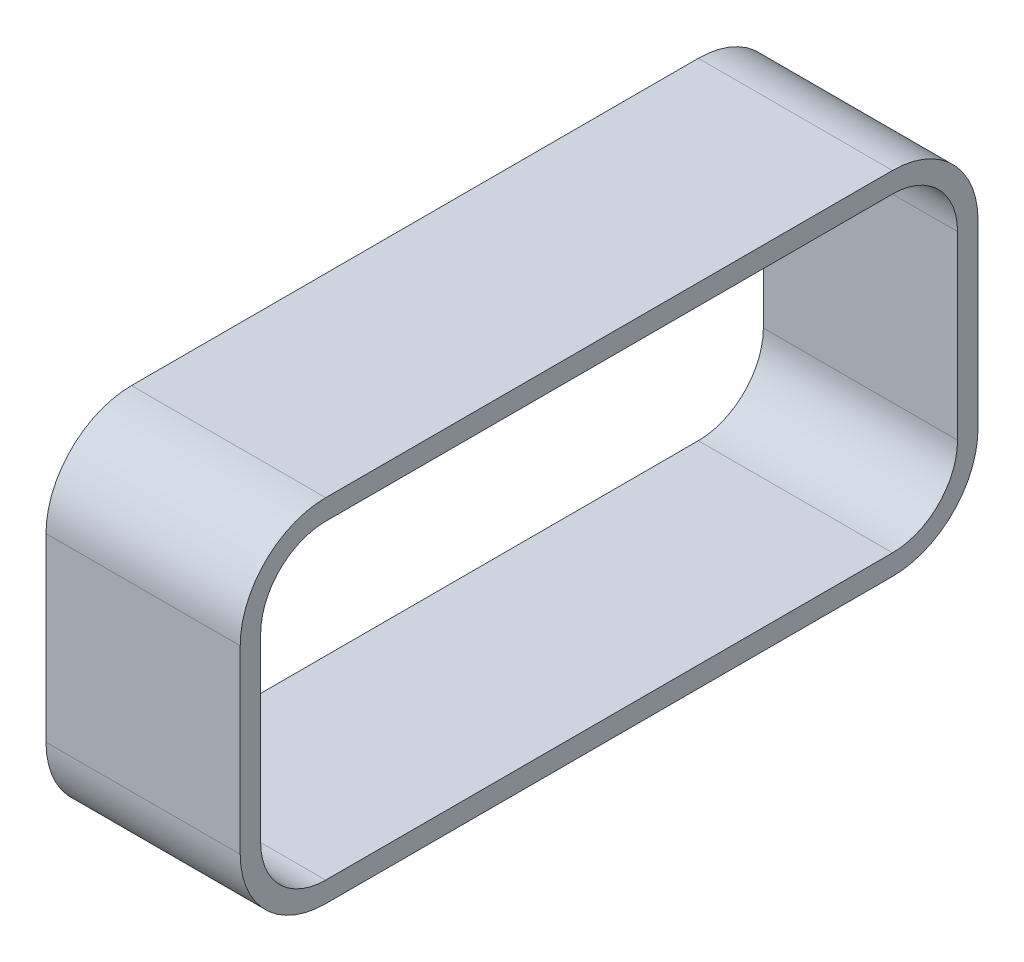
SolidWorks part; units mm, degrees
ref_plane "Front Plane" through (0, 0, 0) normal (0, 0, 1) x (1, 0, 0)
ref_plane "Top Plane" through (0, 0, 0) normal (0, 1, 0) x (1, 0, 0)
ref_plane "Right Plane" through (0, 0, 0) normal (1, 0, 0) x (0, 0, -1)
sketch "Sketch1" plane through (0, 0, 0) normal (1, 0, 0) x (0, 0, -1)
  line L0 (0, 0) -> (3050, 0)
  line L1 (-460, 1322) -> (-460, 350)
  line L2 (3050, 1672) -> (0, 1672)
  line L3 (3400, 1322) -> (3400, 350)
  line L4 (0, 1782) -> (3050, 1782)
  line L5 (3510, 1322) -> (3510, 350)
  line L6 (3050, -110) -> (0, -110)
  line L7 (-350, 350) -> (-350, 1322)
  arc A0 (3050, 0) -> (3400, 350) centre (3050, 350) ccw
  arc A1 (3050, 1672) -> (3400, 1322) centre (3050, 1322) cw
  arc A2 (3050, 1782) -> (3510, 1322) centre (3050, 1322) cw
  arc A3 (3510, 350) -> (3050, -110) centre (3050, 350) cw
  arc A4 (0, 0) -> (-350, 350) centre (0, 350) cw
  arc A5 (-350, 1322) -> (0, 1672) centre (0, 1322) cw
  arc A6 (0, 1782) -> (-460, 1322) centre (0, 1322) ccw
  arc A7 (-460, 350) -> (0, -110) centre (0, 350) ccw
  dimension "D2" = 972
  dimension "D3" = 350
  dimension "D1" = 3050
extrude "Boss-Extrude1" add sketch "Sketch1" along normal blind 1045
